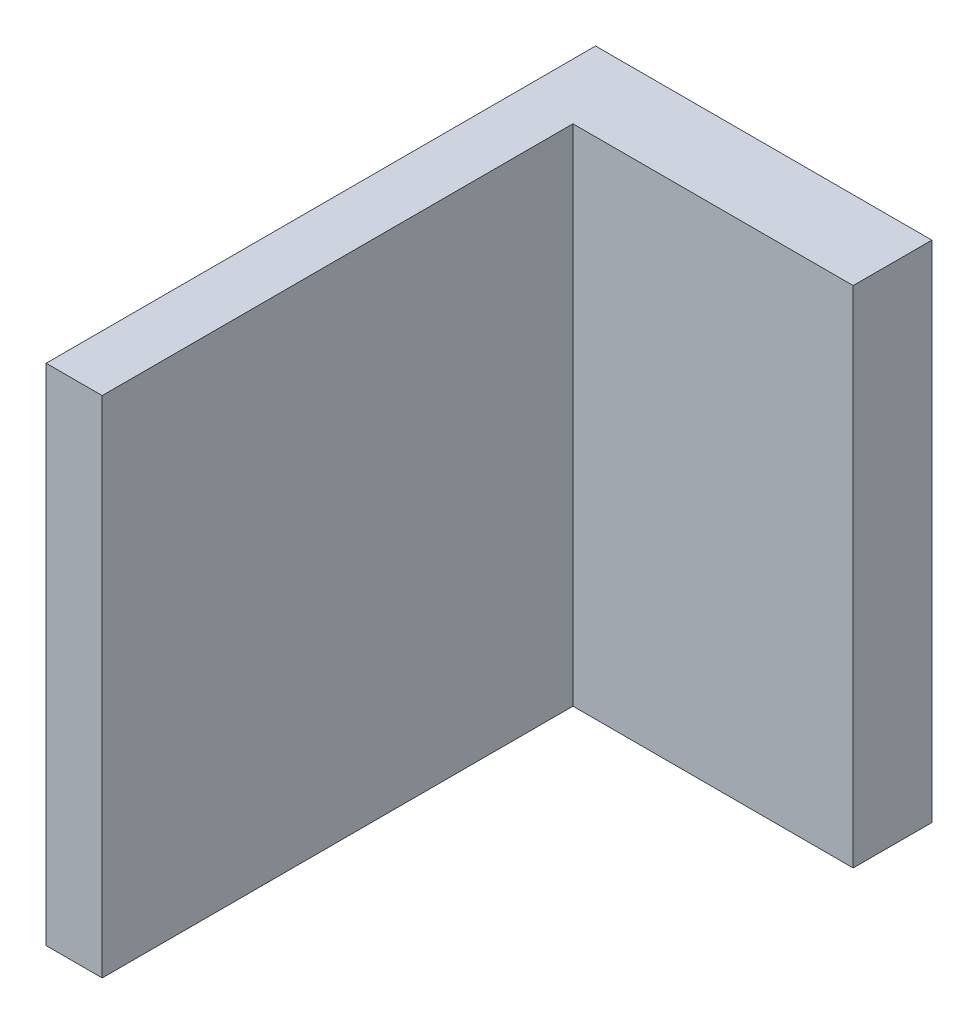
SolidWorks part; units mm, degrees
ref_plane "Front Plane" through (0, 0, 0) normal (0, 0, 1) x (1, 0, 0)
ref_plane "Top Plane" through (0, 0, 0) normal (0, 1, 0) x (1, 0, 0)
ref_plane "Right Plane" through (0, 0, 0) normal (1, 0, 0) x (0, 0, -1)
sketch "Sketch1" plane through (0, 0, 0) normal (0, 1, 0) x (1, 0, 0)
  line L2 (1.2207, 10.2535) -> (1.2207, -10.7465)
  line L3 (1.2207, -10.7465) -> (-1.2793, -10.7465)
  line L4 (-1.2793, 11.2631) -> (-1.2793, -10.7465)
  line L7 (1.2207, 10.2535) -> (13.7207, 10.2535)
  line L8 (-1.2793, 11.2631) -> (-1.2793, 13.7631)
  line L9 (-1.2793, 13.7631) -> (13.7207, 13.7631)
  line L10 (13.7207, 10.2535) -> (13.7207, 13.7631)
  point P0 (0, 0)
  dimension "D1" = 21
  dimension "D2" = 2.5
  dimension "D3" = 2.5
  dimension "D4" = 15
extrude "Boss-Extrude1" add sketch "Sketch1" along normal blind 22.5
